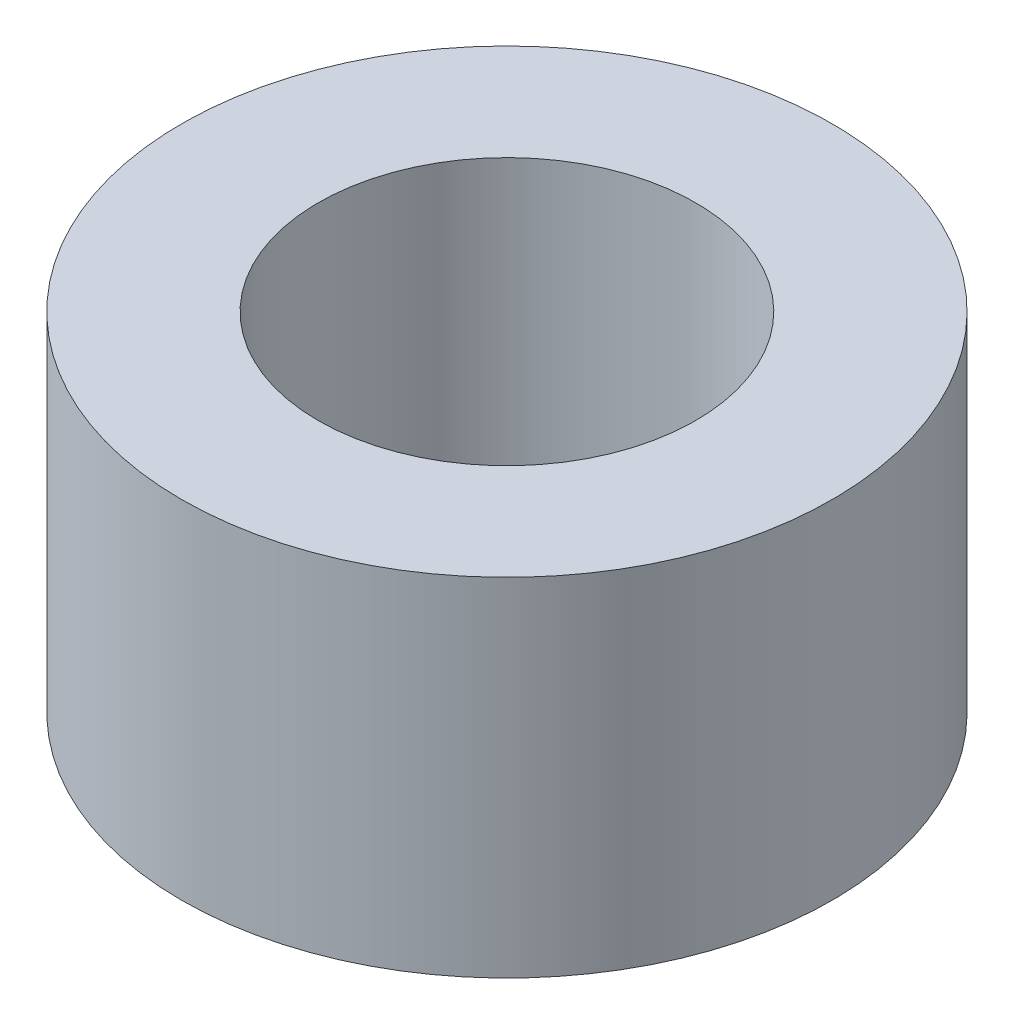
SolidWorks part; units mm, degrees
ref_plane "Front Plane" through (0, 0, 0) normal (0, 0, 1) x (1, 0, 0)
ref_plane "Top Plane" through (0, 0, 0) normal (0, 1, 0) x (1, 0, 0)
ref_plane "Right Plane" through (0, 0, 0) normal (1, 0, 0) x (0, 0, -1)
sketch "Sketch2" plane through (0, 0, 0) normal (0, 1, 0) x (1, 0, 0)
  circle A0 centre (0, 0) radius 7.5
  circle A1 centre (0, 0) radius 4.35
  dimension "D1" = 8.7
  dimension "D2" = 15
extrude "Boss-Extrude1" add sketch "Sketch2" along normal blind 8
